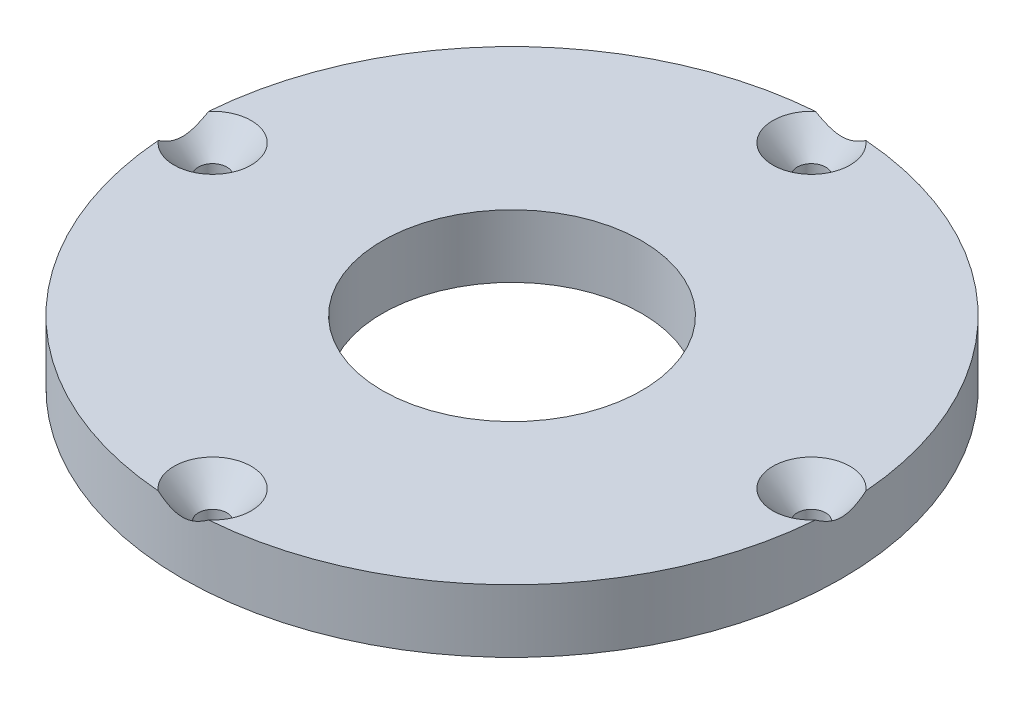
SolidWorks part; units mm, degrees
ref_plane "Front Plane" through (0, 0, 0) normal (0, 0, 1) x (1, 0, 0)
ref_plane "Top Plane" through (0, 0, 0) normal (0, 1, 0) x (1, 0, 0)
ref_plane "Right Plane" through (0, 0, 0) normal (1, 0, 0) x (0, 0, -1)
sketch "Sketch1" plane through (0, 0, 0) normal (0, 1, 0) x (1, 0, 0)
  circle A0 centre (0, 0) radius 33.274
  dimension "D1" = 66.548
extrude "Boss-Extrude1" add sketch "Sketch1" along normal blind 6.35
hole_wizard "PlateMtgScrew" positions "Sketch6" profile "Sketch7" tap size "#6-40" standard "ANSI Inch"
sketch "Sketch6" plane through (0, 6.35, 0) normal (0, 1, 0) x (1, 0, 0)
  circle A0 centre (0, 0) radius 30.226 construction
  point P5 (-30.226, 0)
  point P7 (0, -30.226)
  point P9 (30.226, 0)
  point P10 (0, 30.226)
  dimension "D1" = 60.452
sketch "Sketch7" plane through (0, 6.35, -30.226) normal (1, 0, 0) x (0, 0, 1)
  line L0 (0, 0) -> (0, 11.0477)
  line L1 (0, 11.0477) -> (1.4351, 10.1854)
  line L2 (1.4351, 10.1854) -> (1.4351, 2.8343)
  line L3 (1.4351, 2.8343) -> (3.8989, 0)
  line L5 (3.8989, 0) -> (0, 0)
  line L6 (-1.4351, 2.8343) -> (-3.8989, 0) construction
  line L10 (0, 11.0477) -> (-1.4351, 10.1854) construction
  line L11 (0, -6.35) -> (0, 107.95) construction
  dimension "Tap Drill Dia." = 2.8702
  dimension "Tap Drill Depth" = 10.1854
  dimension "Near C'Sink Dia." = 7.7978
  dimension "Near C'Sink Angle" = 82
  dimension "Drill Angle" = 118
cosmetic thread "Hole Thread5"
cosmetic thread "Hole Thread6"
cosmetic thread "Hole Thread7"
cosmetic thread "Hole Thread8"
hole_wizard "ShaftBore" positions "Sketch10" profile "Sketch11" legacy end condition through all
sketch "Sketch10" plane through (0, 6.35, 0) normal (0, 1, 0) x (1, 0, 0)
  point P0 (0, 0)
sketch "Sketch11" plane through (0, 6.35, 0) normal (1, 0, 0) x (0, 0, 1)
  line L0 (0, 0) -> (0, 14.2194)
  line L1 (0, 14.2194) -> (13.0969, 6.35)
  line L2 (13.0969, 6.35) -> (13.0969, 0)
  line L4 (13.0969, 0) -> (0, 0)
  line L6 (0, 14.2194) -> (-13.0969, 6.35) construction
  line L7 (0, -4.2442) -> (0, 117.3081) construction
  dimension "Diameter" = 26.1937
  dimension "Depth" = 6.35
  dimension "Drill Angle" = 118
